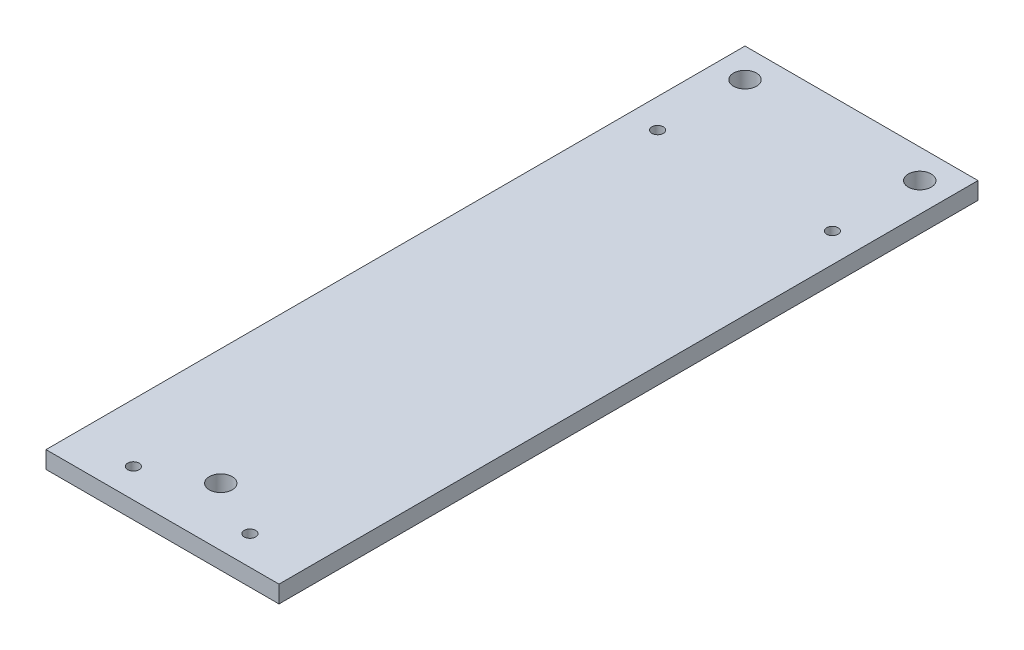
SolidWorks part; units mm, degrees
ref_plane "Front Plane" through (0, 0, 0) normal (0, 0, 1) x (1, 0, 0)
ref_plane "Top Plane" through (0, 0, 0) normal (0, 1, 0) x (1, 0, 0)
ref_plane "Right Plane" through (0, 0, 0) normal (1, 0, 0) x (0, 0, -1)
sketch "Sketch1" plane through (0, 0, 0) normal (0, 1, 0) x (1, 0, 0)
  line L0 (0, 10.16) -> (60.96, 10.16) construction
  line L1 (0, 0) -> (60.96, 0)
  line L2 (0, 0) -> (0, 20.32)
  line L3 (0, 20.32) -> (60.96, 20.32)
  line L4 (60.96, 0) -> (60.96, 20.32)
  line L5 (30.48, 0) -> (30.48, 20.32) construction
  line L6 (60.96, 20.32) -> (96.52, 20.32)
  line L7 (58.42, 17.78) -> (58.42, 2.54) construction
  line L8 (96.52, 20.32) -> (96.52, 0)
  line L9 (96.52, 0) -> (76.2, 0)
  line L10 (76.2, 0) -> (76.2, 20.32)
  line L11 (96.52, 0) -> (96.52, -76.2)
  line L12 (96.52, -76.2) -> (0, -76.2)
  line L13 (0, -76.2) -> (0, 0)
  line L14 (0, -15.24) -> (20.32, -15.24)
  line L15 (20.32, -15.24) -> (20.32, -76.2)
  line L16 (25.4, -76.2) -> (25.4, -15.24)
  line L17 (25.4, -15.24) -> (45.72, -15.24)
  line L18 (45.72, -15.24) -> (45.72, -76.2)
  line L19 (96.52, -15.24) -> (76.2, -15.24)
  line L20 (76.2, -15.24) -> (76.2, -76.2)
  line L21 (50.8, -76.2) -> (50.8, -15.24)
  line L22 (50.8, -15.24) -> (71.12, -15.24)
  line L23 (71.12, -15.24) -> (71.12, -76.2)
  line L24 (76.2, 10.16) -> (83.7042, 10.16) construction
  line L25 (86.36, 0) -> (86.36, 7.3478) construction
  line L26 (93.98, 17.78) -> (93.98, 2.54) construction
  line L27 (10.16, -15.24) -> (10.16, -29.4159) construction
  line L28 (20.32, -45.72) -> (11.2685, -45.72) construction
  line L29 (2.54, -73.66) -> (17.78, -73.66) construction
  line L30 (17.78, -17.78) -> (17.78, -25.4) construction
  line L31 (48.26, -76.2) -> (48.26, -12.1893) construction
  line L32 (35.56, -15.24) -> (35.56, -27.7258) construction
  line L33 (60.96, -63.5) -> (60.96, -71.12) construction
  line L34 (78.74, 17.78) -> (93.98, 17.78) construction
  line L35 (78.74, 2.54) -> (78.74, 17.78) construction
  circle A0 centre (2.54, 2.54) radius 1
  circle A1 centre (58.42, 2.54) radius 1
  circle A2 centre (58.42, 17.78) radius 1
  circle A3 centre (2.54, 17.78) radius 1
  circle A4 centre (22.86, 5.08) radius 0.5
  circle A5 centre (53.34, 10.16) radius 0.5
  circle A6 centre (22.86, 15.24) radius 0.5
  circle A7 centre (93.98, 17.78) radius 1
  circle A8 centre (93.98, 2.54) radius 1
  circle A9 centre (78.74, 2.54) radius 1
  circle A10 centre (78.74, 17.78) radius 1
  circle A11 centre (93.98, 10.16) radius 0.5
  circle A12 centre (2.54, -17.78) radius 1
  circle A13 centre (17.78, -17.78) radius 1
  circle A14 centre (17.78, -73.66) radius 1
  circle A15 centre (2.54, -73.66) radius 1
  circle A16 centre (17.78, -25.4) radius 0.5
  circle A17 centre (10.16, -73.66) radius 0.5
  circle A18 centre (2.54, -25.4) radius 0.5
  circle A19 centre (78.74, -73.66) radius 1
  circle A20 centre (86.36, -73.66) radius 0.5
  circle A21 centre (93.98, -73.66) radius 1
  circle A22 centre (78.74, -25.4) radius 0.5
  circle A23 centre (78.74, -17.78) radius 1
  circle A24 centre (93.98, -25.4) radius 0.5
  circle A25 centre (93.98, -17.78) radius 1
  circle A26 centre (53.34, -17.78) radius 1
  circle A27 centre (53.34, -25.4) radius 0.5
  circle A28 centre (68.58, -25.4) radius 0.5
  circle A29 centre (68.58, -17.78) radius 1
  circle A30 centre (60.96, -71.12) radius 1
  circle A31 centre (60.96, -63.5) radius 0.5
  circle A32 centre (35.56, -71.12) radius 1
  circle A33 centre (27.94, -17.78) radius 1
  circle A34 centre (27.94, -25.4) radius 0.5
  circle A35 centre (43.18, -25.4) radius 0.5
  circle A36 centre (43.18, -17.78) radius 1
  circle A37 centre (30.48, -73.66) radius 0.5
  circle A38 centre (40.64, -73.66) radius 0.5
  circle A39 centre (87.884, 17.78) radius 0.5
  circle A40 centre (85.344, 17.78) radius 0.5
  circle A41 centre (78.74, 11.176) radius 0.5
  circle A42 centre (78.74, 8.636) radius 0.5
  dimension "D3" = 2
  dimension "D6" = 1
  dimension "D8" = 7.62
  dimension "D13" = 2.54
  dimension "D18" = 2.54
  dimension "D19" = 10.16
  dimension "D20" = 2.54
  dimension "D21" = 10.16
  dimension "D24" = 5.08
  dimension "D25" = 2.54
  dimension "D26" = 2.54
  dimension "D27" = 2.54
  dimension "D1" = 60.96
  dimension "D2" = 20.32
  dimension "D4" = 2.54
  dimension "D5" = 2.54
  dimension "D7" = 22.86
  dimension "D9" = 5.08
  dimension "D10" = 15.24
  dimension "D11" = 20.32
  dimension "D12" = 5.08
  dimension "D14" = 5.08
  dimension "D15" = 60.96
  dimension "D16" = 15.24
  dimension "D17" = 2.54
  dimension "D22" = 5.08
  dimension "D23" = 7.62
  dimension "D28" = 9.144
  dimension "D29" = 9.144
extrude "Boss-Extrude1" add sketch "Sketch1" along normal blind 1.5 contours L18 L17 L16 L12 A36 A35 A32 A33 A34 A37 A38
